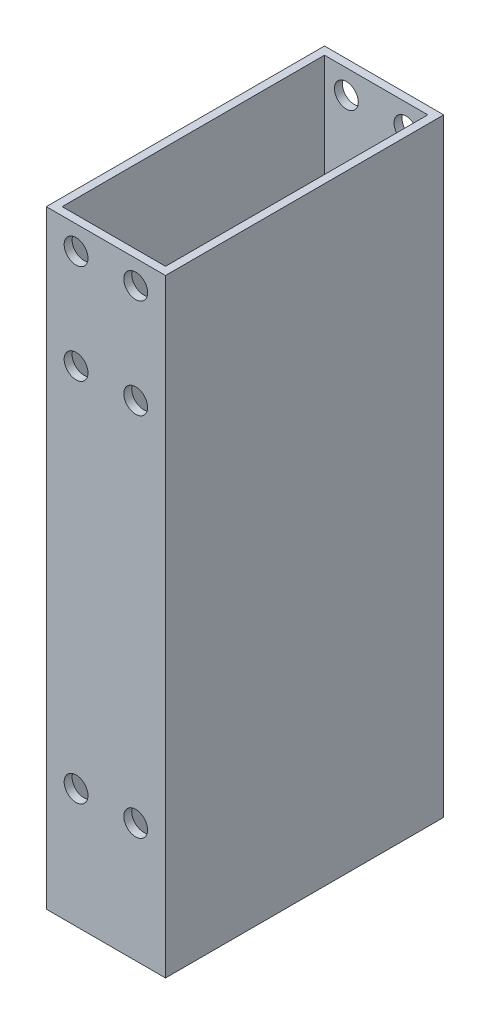
SolidWorks part; units mm, degrees
ref_plane "前视基准面" through (0, 0, 0) normal (0, 0, 1) x (1, 0, 0)
ref_plane "上视基准面" through (0, 0, 0) normal (0, 1, 0) x (1, 0, 0)
ref_plane "右视基准面" through (0, 0, 0) normal (1, 0, 0) x (0, 0, -1)
other "Configuration Table"
sketch "草图1" plane through (0, 0, 0) normal (0, 0, 1) x (1, 0, 0)
  line L1 (15, -383.07) -> (-15, -383.07)
  line L2 (15, -383.07) -> (15, 383.07)
  line L3 (15, 383.07) -> (-15, 383.07)
  line L4 (-15, -383.07) -> (-15, 383.07)
  line L5 (15, -383.07) -> (-15, 383.07) construction
  line L6 (15, 383.07) -> (-15, -383.07) construction
  circle A0 centre (-7.5, 377.0748) radius 2
  circle A1 centre (7.5, 377.0748) radius 2
  circle A2 centre (-7.5, 352.0748) radius 2
  circle A3 centre (7.5, 352.0748) radius 2
  circle A4 centre (7.4999, 260) radius 2 construction
  circle A5 centre (-7.5001, 260) radius 2 construction
  circle A6 centre (7.4999, 260) radius 2
  circle A7 centre (-7.5001, 260) radius 2
  point P0 (0, 0)
  dimension "D1" = 30
  dimension "D2" = 766.14
extrude "凸台-拉伸2" add sketch "草图1" along normal blind 70
sketch "草图2" plane through (0, -383.07, 0) normal (0, -1, 0) x (1, 0, 0)
  line L0 (-15, 70) -> (-15, 0) construction
  line L1 (-13, 68) -> (13, 68)
  line L2 (-13, 68) -> (-13, 2)
  line L3 (-13, 2) -> (13, 2)
  line L4 (13, 68) -> (13, 2)
  line L5 (-13, 68) -> (13, 2) construction
  line L6 (-13, 2) -> (13, 68) construction
  line L7 (-15, 70) -> (15, 70) construction
  line L8 (15, 70) -> (15, 0) construction
  line L9 (-15, 0) -> (15, 0) construction
  point P0 (0, 35)
  dimension "D1" = 2
  dimension "D2" = 2
  dimension "D3" = 2
  dimension "D4" = 2
extrude "切除-拉伸3" cut sketch "草图2" against normal through all contours L2 L1 L4 L3
sketch "草图3" plane through (0, 0, 70) normal (0, 0, 1) x (1, 0, 0)
  line L0 (-15, 230) -> (15, 230)
  line L1 (-15, 383.07) -> (-15, -383.07) construction
  line L2 (15, -383.07) -> (15, 383.07) construction
  line L3 (15, 383.07) -> (-15, 383.07) construction
  line L4 (-15, 230) -> (-15, -394.9368)
  line L5 (-15, -394.9368) -> (15, -394.9368)
  line L6 (15, -394.9368) -> (15, 230)
  dimension "D1" = 153.07
extrude "切除-拉伸4" cut sketch "草图3" against normal through all
sketch "草图4" plane through (0, 0, 70) normal (0, 0, 1) x (1, 0, 0)
  circle A0 centre (-7.5, 377.0748) radius 3
  circle A1 centre (7.5, 377.0748) radius 3
  circle A2 centre (7.5, 352.0748) radius 3
  circle A3 centre (-7.5, 352.0748) radius 3
  circle A4 centre (-7.5001, 260) radius 3
  circle A5 centre (7.4999, 260) radius 3
  dimension "D1" = 6
  dimension "D2" = 6
  dimension "D3" = 6
  dimension "D4" = 6
  dimension "D5" = 6
  dimension "D6" = 6
extrude "切除-拉伸5" cut sketch "草图4" against normal blind 115
